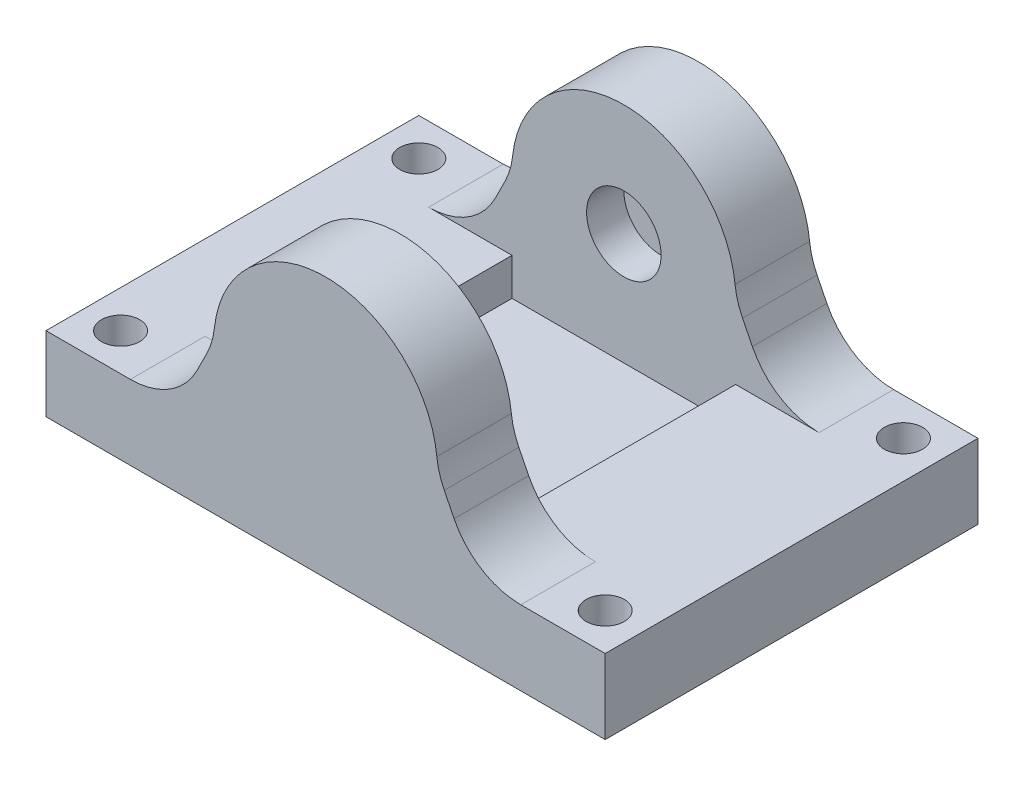
SolidWorks part; units mm, degrees
ref_plane "Front Plane" through (0, 0, 0) normal (0, 0, 1) x (1, 0, 0)
ref_plane "Top Plane" through (0, 0, 0) normal (0, 1, 0) x (1, 0, 0)
ref_plane "Right Plane" through (0, 0, 0) normal (1, 0, 0) x (0, 0, -1)
sketch "Sketch1" plane through (0, 0, 0) normal (0, 1, 0) x (1, 0, 0)
  line L1 (0, 0) -> (75, 0)
  line L2 (0, 0) -> (0, 50)
  line L3 (0, 50) -> (75, 50)
  line L4 (75, 0) -> (75, 50)
  dimension "D1" = 75
  dimension "D2" = 50
extrude "Boss-Extrude1" add sketch "Sketch1" along normal blind 10 contours L4 L3 L2 L1
sketch "Sketch2" plane through (0, 0, 0) normal (0, 0, 1) x (1, 0, 0)
  line L0 (0, 10) -> (75, 10) construction
  line L1 (75, 10) -> (75, 0) construction
  line L2 (52.5, 20) -> (57.5, 10)
  line L3 (22.5, 20) -> (17.5, 10)
  line L4 (17.5, 10) -> (57.5, 10)
  arc A0 (52.5, 20) -> (22.5, 20) centre (37.5, 20) ccw
  dimension "D1" = 30
  dimension "D2" = 10
  dimension "D3" = 37.5
  dimension "D4" = 5
  dimension "D5" = 5
extrude "Boss-Extrude2" add sketch "Sketch2" against normal blind 10
fillet "Fillet1" radius 10 4 edges at (17.5, 10, -5) (57.5, 10, -5) (22.5, 20, -5) (52.5, 20, -5)
sketch "Sketch4" plane through (0, 0, -10) normal (0, 0, -1) x (-1, 0, 0)
  line L0 (-11.3197, 10) -> (-63.6803, 10) construction
  circle A0 centre (-37.5, 20) radius 5
  dimension "D1" = 10
  dimension "D2" = 10
  dimension "D3" = 37.5
extrude "Cut-Extrude1" cut sketch "Sketch4" against normal blind 5
ref_plane "Plane1" through (0, 0, -25) normal (0, 0, -1) x (-1, 0, 0)
mirror "Mirror1" about plane through (0, 0, -25) normal (0, 0, -1) of "Boss-Extrude2", "Fillet1", "Cut-Extrude1"
sketch "Sketch5" plane through (0, 10, 0) normal (0, 1, 0) x (1, 0, 0)
  line L0 (0, 0) -> (0, 50) construction
  line L1 (0, 0) -> (11.3197, 0) construction
  circle A0 centre (5, 5) radius 2.5625
  dimension "D1" = 5.125
  dimension "D2" = 5
  dimension "D3" = 5
extrude "Cut-Extrude2" cut sketch "Sketch5" against normal through all contours A0
ref_plane "Plane2" through (37.5, 0, 0) normal (1, 0, 0) x (0, 0, -1)
mirror "Mirror2" about plane through (0, 0, -25) normal (0, 0, -1) of "Cut-Extrude2"
mirror "Mirror3" about plane through (37.5, 0, 0) normal (1, 0, 0) of "Mirror2", "Cut-Extrude2"
sketch "Sketch6" plane through (0, 10, 0) normal (0, 1, 0) x (1, 0, 0)
  line L0 (11.3197, 40) -> (63.6803, 40) construction
  line L1 (63.6803, 10) -> (54.7361, 10) construction
  line L2 (22.5, 40) -> (52.5, 40)
  line L3 (22.5, 40) -> (22.5, 10)
  line L4 (22.5, 10) -> (52.5, 10)
  line L5 (52.5, 40) -> (52.5, 10)
  line L6 (37.5, -5.5) -> (37.5, 5.5) construction
  dimension "D1" = 30
  dimension "D2" = 15
extrude "Cut-Extrude3" cut sketch "Sketch6" against normal blind 5
